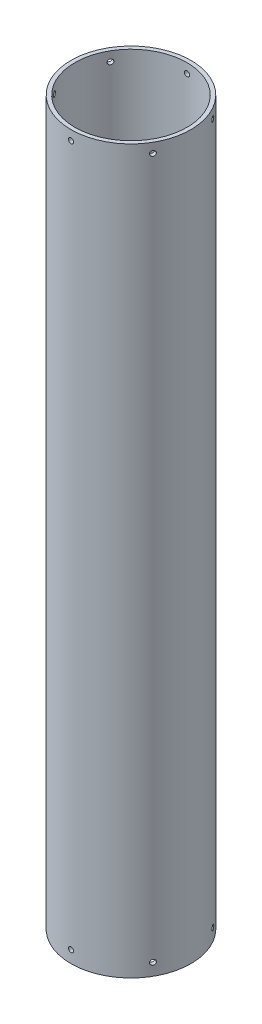
SolidWorks part; units mm, degrees
ref_plane "Front Plane" through (0, 0, 0) normal (0, 0, 1) x (1, 0, 0)
ref_plane "Top Plane" through (0, 0, 0) normal (0, 1, 0) x (1, 0, 0)
ref_plane "Right Plane" through (0, 0, 0) normal (1, 0, 0) x (0, 0, -1)
sketch "Sketch2" plane through (0, 0, 0) normal (0, 1, 0) x (1, 0, 0)
  circle A0 centre (0, 0) radius 18
  circle A1 centre (0, 0) radius 19.25
  dimension "D1" = 1.25
extrude "Boss-Extrude1" add sketch "Sketch2" along normal blind 231.82
sketch "Sketch3" plane through (0, 0, 0) normal (0, 0, 1) x (1, 0, 0)
  circle A0 centre (0, 3.92) radius 0.815
  dimension "D2" = 1.63
  dimension "D1" = 3.92
extrude "Cut-Extrude2" cut sketch "Sketch3" against normal blind 231.82 contours A0
pattern_circular "CirPattern3" count 6 over 360 about axis through (0, 231.82, 0) along (0, -1, 0) of "Cut-Extrude2"
sketch "Sketch4" plane through (0, 0, 0) normal (0, 0, 1) x (1, 0, 0)
  line L1 (19.25, 231.82) -> (-19.25, 231.82) construction
  circle A1 centre (0, 228.73) radius 0.815
  dimension "D2" = 1.63
  dimension "D1" = 3.09
extrude "Cut-Extrude3" cut sketch "Sketch4" along normal blind 231.82
pattern_circular "CirPattern4" count 6 over 360 about axis through (0, 231.82, 0) along (0, -1, 0) of "Cut-Extrude3"
